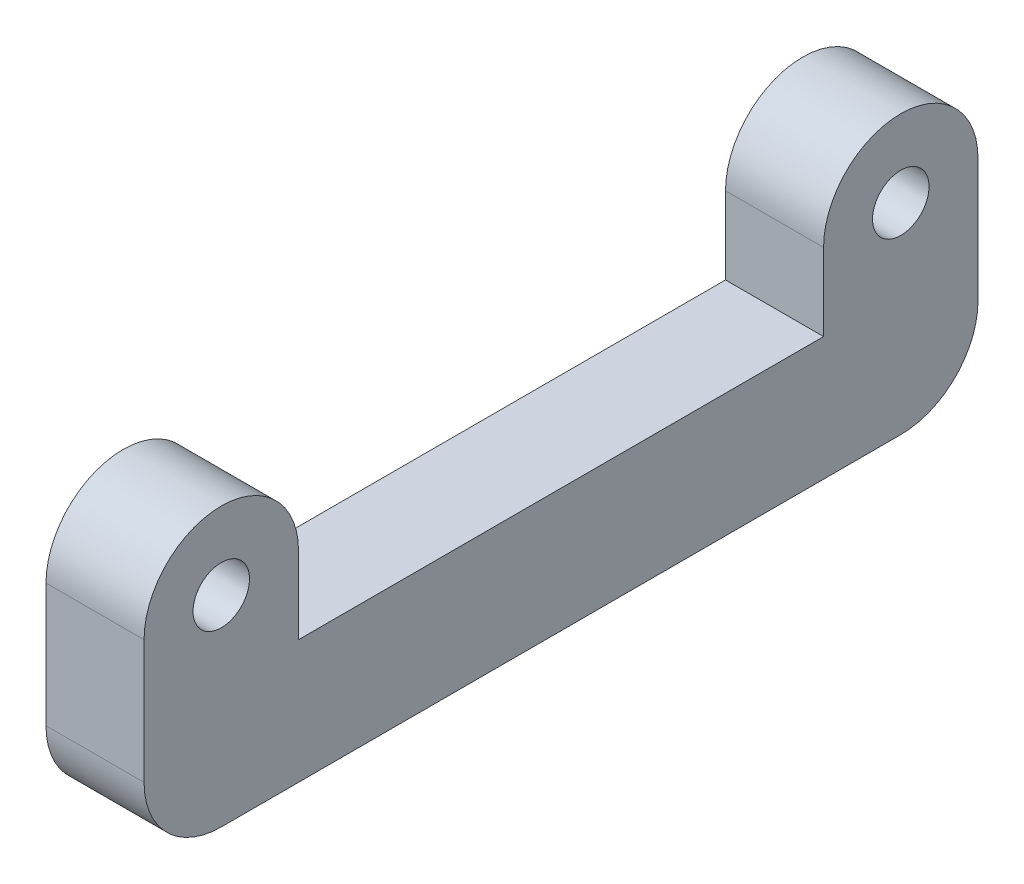
SolidWorks part; units mm, degrees
ref_plane "Front Plane" through (0, 0, 0) normal (0, 0, 1) x (1, 0, 0)
ref_plane "Top Plane" through (0, 0, 0) normal (0, 1, 0) x (1, 0, 0)
ref_plane "Right Plane" through (0, 0, 0) normal (1, 0, 0) x (0, 0, -1)
sketch "Sketch1" plane through (0, 0, 0) normal (1, 0, 0) x (0, 0, -1)
  line L0 (-27, -4) -> (-27, 4)
  line L1 (-27, -4) -> (27, -4)
  line L2 (-17, 4) -> (17, 4)
  line L3 (27, -4) -> (27, 4)
  line L4 (-27, -4) -> (27, 4) construction
  line L5 (-27, 4) -> (27, -4) construction
  line L8 (-27, 4) -> (-27, 9)
  line L9 (-27, 9) -> (-17, 9) construction
  line L10 (-17, 4) -> (-17, 9)
  line L12 (27, 4) -> (27, 9)
  line L13 (27, 9) -> (17, 9) construction
  line L14 (17, 4) -> (17, 9)
  arc A0 (-27, 9) -> (-17, 9) centre (-22, 9) cw
  arc A1 (17, 9) -> (27, 9) centre (22, 9) cw
  point P1 (0, 0)
  point P12 (-22, 9)
  point P13 (22, 9)
  dimension "D1" = 8
  dimension "D2" = 34
  dimension "D3" = 44
  dimension "D4" = 5
extrude "Boss-Extrude1" add sketch "Sketch1" along normal blind 6.35
fillet "Fillet1" radius 5 2 edges at (3.175, -4, -27) (3.175, -4, 27)
hole_wizard "#6 Clearance Hole1" positions "Sketch3" profile "Sketch2" hole size "#6" standard "ANSI Inch" end condition through all
sketch "Sketch3" plane through (0, 0, 0) normal (-1, 0, 0) x (0, 0, 1)
  point P0 (-22, 9)
  point P3 (22, 9)
sketch "Sketch2" plane through (0, 9, -22) normal (0, 1, 0) x (0, 0, 1)
  line L0 (0, 0) -> (0, 6.35)
  line L1 (0, 6.35) -> (1.8288, 6.35)
  line L2 (1.8288, 6.35) -> (1.8288, 0)
  line L5 (1.8288, 0) -> (0, 0)
  line L11 (0, -6.35) -> (0, 107.95) construction
  dimension "Thru Hole Dia." = 3.6576
  dimension "Thru Hole Depth" = 6.35
